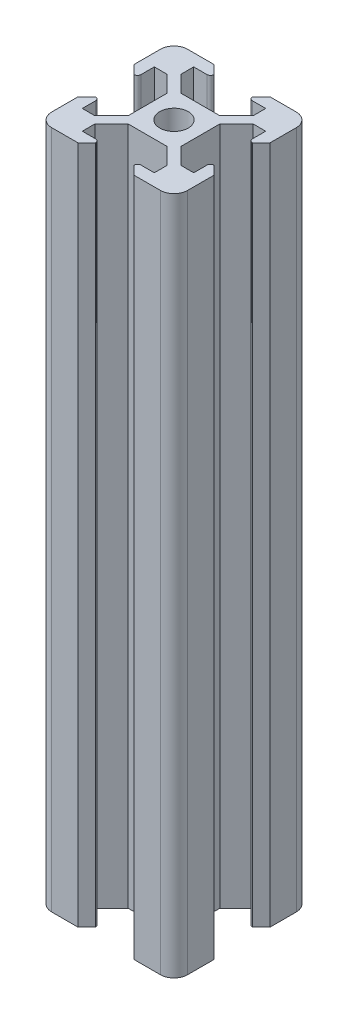
SolidWorks part; units mm, degrees
material "6063-T6"
ref_plane "Alzado" through (0, 0, 0) normal (0, 0, 1) x (1, 0, 0)
ref_plane "Planta" through (0, 0, 0) normal (0, 1, 0) x (1, 0, 0)
ref_plane "Vista lateral" through (0, 0, 0) normal (1, 0, 0) x (0, 0, -1)
sketch "Croquis1" plane through (0, 0, 0) normal (0, 1, 0) x (1, 0, 0)
  line L0 (0, 0) -> (-10, 10) construction
  line L1 (3.9, -2.84) -> (3.9, 2.84)
  line L2 (8.2, 5.3) -> (8.2, 3.34)
  line L3 (10, 8) -> (10, 4.14)
  line L4 (8.2, 5.3) -> (6.36, 5.3)
  line L5 (3.9, 2.84) -> (6.36, 5.3)
  line L6 (8.7, 2.84) -> (10, 4.14)
  line L7 (0, 0) -> (10, 10) construction
  line L8 (8, 10) -> (4.14, 10)
  line L9 (2.84, 8.7) -> (4.14, 10)
  line L10 (5.3, 8.2) -> (3.34, 8.2)
  line L11 (5.3, 8.2) -> (5.3, 6.36)
  line L12 (2.84, 3.9) -> (5.3, 6.36)
  line L13 (-2.84, 3.9) -> (2.84, 3.9)
  line L14 (-2.84, -3.9) -> (-5.3, -6.36)
  line L15 (-30.7915, 0) -> (30.7915, 0) construction
  line L16 (3.9, -2.84) -> (6.36, -5.3)
  line L17 (8.2, -5.3) -> (6.36, -5.3)
  line L18 (8.2, -5.3) -> (8.2, -3.34)
  line L19 (8.7, -2.84) -> (10, -4.14)
  line L20 (10, -8) -> (10, -4.14)
  line L21 (8, -10) -> (4.14, -10)
  line L22 (2.84, -8.7) -> (4.14, -10)
  line L23 (5.3, -8.2) -> (3.34, -8.2)
  line L24 (5.3, -8.2) -> (5.3, -6.36)
  line L25 (2.84, -3.9) -> (5.3, -6.36)
  line L26 (-2.84, -3.9) -> (2.84, -3.9)
  line L27 (0, 0) -> (0, 15.4885) construction
  line L28 (0, 0) -> (0, -17.6665) construction
  line L29 (0, 0) -> (-18.0561, 0) construction
  line L30 (-5.3, -8.2) -> (-5.3, -6.36)
  line L31 (-5.3, -8.2) -> (-3.34, -8.2)
  line L32 (-2.84, -8.7) -> (-4.14, -10)
  line L33 (-8, -10) -> (-4.14, -10)
  line L34 (-10, -8) -> (-10, -4.14)
  line L35 (-8.7, -2.84) -> (-10, -4.14)
  line L36 (-8.2, -5.3) -> (-8.2, -3.34)
  line L37 (-8.2, -5.3) -> (-6.36, -5.3)
  line L38 (-3.9, -2.84) -> (-6.36, -5.3)
  line L39 (-2.84, 3.9) -> (-5.3, 6.36)
  line L40 (-5.3, 8.2) -> (-5.3, 6.36)
  line L41 (-5.3, 8.2) -> (-3.34, 8.2)
  line L42 (-2.84, 8.7) -> (-4.14, 10)
  line L43 (-8, 10) -> (-4.14, 10)
  line L44 (-8.7, 2.84) -> (-10, 4.14)
  line L45 (-3.9, 2.84) -> (-6.36, 5.3)
  line L46 (-8.2, 5.3) -> (-6.36, 5.3)
  line L47 (-10, 8) -> (-10, 4.14)
  line L48 (-8.2, 5.3) -> (-8.2, 3.34)
  line L49 (-3.9, -2.84) -> (-3.9, 2.84)
  arc A0 (8.2, 3.34) -> (8.7, 2.84) centre (8.7, 3.34) ccw
  arc A1 (3.34, 8.2) -> (2.84, 8.7) centre (3.34, 8.7) cw
  arc A2 (10, 8) -> (8, 10) centre (8, 8) ccw
  arc A3 (8.2, -3.34) -> (8.7, -2.84) centre (8.7, -3.34) cw
  arc A4 (10, -8) -> (8, -10) centre (8, -8) cw
  arc A5 (3.34, -8.2) -> (2.84, -8.7) centre (3.34, -8.7) ccw
  arc A6 (-3.34, -8.2) -> (-2.84, -8.7) centre (-3.34, -8.7) cw
  arc A7 (-10, -8) -> (-8, -10) centre (-8, -8) ccw
  arc A8 (-8.2, -3.34) -> (-8.7, -2.84) centre (-8.7, -3.34) ccw
  arc A9 (-10, 8) -> (-8, 10) centre (-8, 8) cw
  arc A10 (-3.34, 8.2) -> (-2.84, 8.7) centre (-3.34, 8.7) ccw
  arc A11 (-8.2, 3.34) -> (-8.7, 2.84) centre (-8.7, 3.34) cw
  circle A12 centre (0, 0) radius 2.1
  point P11 (8.2, 2.84)
  point P65 (0, -3.9)
  point P73 (0, 3.9)
  point P80 (-8.2, 2.84)
  dimension "D9" = 0.5
  dimension "D12" = 2
  dimension "D13" = 4.2
  dimension "D2" = 3.9
  dimension "D3" = 3.9
  dimension "D4" = 2.46
  dimension "D5" = 5.86
  dimension "D6" = 1.96
  dimension "D7" = 0.7495
  dimension "D8" = 10
  dimension "D10" = 1.84
  dimension "D11" = 1.3
extrude "Saliente-Extruir2" add sketch "Croquis1" along normal blind 100
